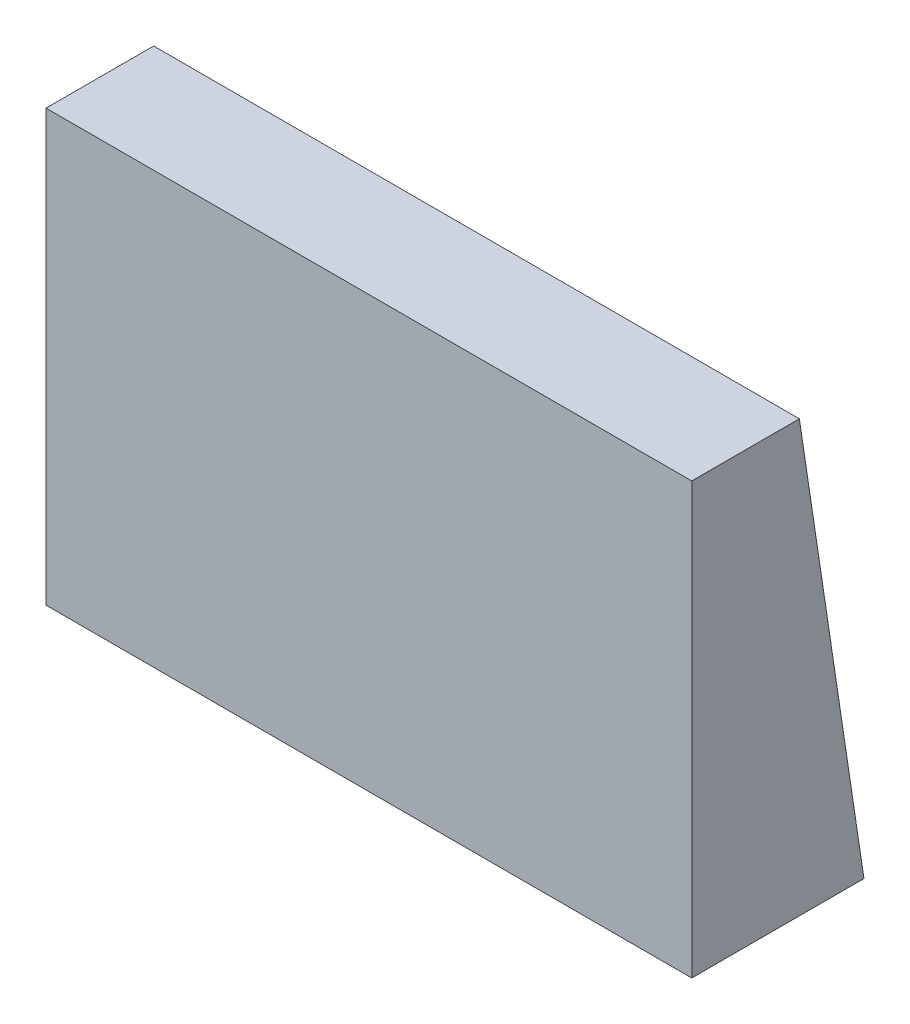
SolidWorks part; units mm, degrees
ref_plane "Front Plane" through (0, 0, 0) normal (0, 0, 1) x (1, 0, 0)
ref_plane "Top Plane" through (0, 0, 0) normal (0, 1, 0) x (1, 0, 0)
ref_plane "Right Plane" through (0, 0, 0) normal (1, 0, 0) x (0, 0, -1)
sketch "Sketch1" plane through (0, 0, 0) normal (0, 1, 0) x (1, 0, 0)
  line L1 (-15, 2.5) -> (15, 2.5)
  line L2 (-15, 2.5) -> (-15, -2.5)
  line L3 (-15, -2.5) -> (15, -2.5)
  line L4 (15, 2.5) -> (15, -2.5)
  line L5 (-15, 2.5) -> (15, -2.5) construction
  line L6 (-15, -2.5) -> (15, 2.5) construction
  point P0 (0, 0)
extrude "Boss-Extrude1" add sketch "Sketch1" along normal blind 20
sketch "Sketch2" plane through (15, 0, 0) normal (1, 0, 0) x (0, 0, -1)
  line L0 (2.5, 0) -> (5.5, 0)
  line L1 (5.5, 0) -> (2.5, 20)
  line L2 (2.5, 20) -> (2.5, 0)
extrude "Boss-Extrude2" add sketch "Sketch2" against normal up to surface (30 mm away) up to face at (-15, 10, 0)
